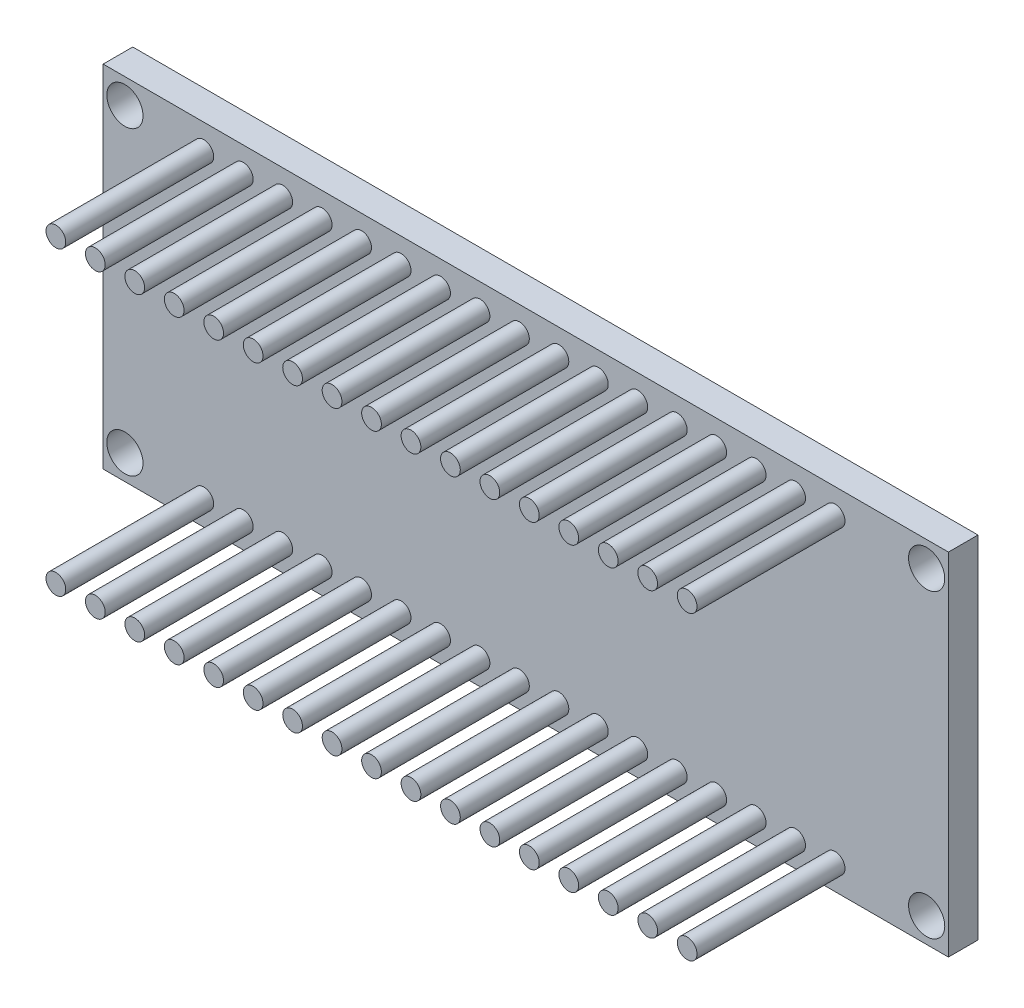
SolidWorks part; units mm, degrees
ref_plane "Front Plane" through (0, 0, 0) normal (0, 0, 1) x (1, 0, 0)
ref_plane "Top Plane" through (0, 0, 0) normal (0, 1, 0) x (1, 0, 0)
ref_plane "Right Plane" through (0, 0, 0) normal (1, 0, 0) x (0, 0, -1)
sketch "Sketch1" plane through (0, 0, 0) normal (0, 0, 1) x (1, 0, 0)
  line L0 (-219.0854, 61.6535) -> (-176.2406, 61.6535) construction
  line L1 (-176.2406, 70.5435) -> (-219.0854, 70.5435)
  line L2 (-176.2406, 70.5435) -> (-176.2406, 52.7635)
  line L3 (-176.2406, 52.7635) -> (-219.0854, 52.7635)
  line L4 (-219.0854, 70.5435) -> (-219.0854, 52.7635)
  line L5 (-197.663, 70.5435) -> (-197.663, 52.7635) construction
  circle A0 centre (-217.983, 69.2785) radius 0.9174
  circle A1 centre (-217.983, 54.0285) radius 0.9174
  circle A2 centre (-177.343, 54.0285) radius 0.9174
  circle A3 centre (-177.343, 69.2785) radius 0.9174
extrude "Boss-Extrude1" add sketch "Sketch1" along normal blind 1.5
sketch "Sketch2" plane through (0, 0, 1.5) normal (0, 0, 1) x (1, 0, 0)
  line L0 (-217.983, 69.2785) -> (-177.343, 69.2785) construction
  line L1 (-219.0854, 61.6535) -> (-203.7997, 61.6535) construction
  line L2 (-219.0854, 70.5435) -> (-219.0854, 52.7635) construction
  circle A0 centre (-213.983, 69.2785) radius 0.5
  circle A2 centre (-213.983, 54.0285) radius 0.5
  circle A3 centre (-211.983, 69.2785) radius 0.5
  circle A4 centre (-211.983, 54.0285) radius 0.5
  circle A5 centre (-209.983, 69.2785) radius 0.5
  circle A6 centre (-209.983, 54.0285) radius 0.5
  circle A7 centre (-207.983, 69.2785) radius 0.5
  circle A8 centre (-207.983, 54.0285) radius 0.5
  circle A9 centre (-205.983, 69.2785) radius 0.5
  circle A10 centre (-205.983, 54.0285) radius 0.5
  circle A11 centre (-203.983, 69.2785) radius 0.5
  circle A12 centre (-203.983, 54.0285) radius 0.5
  circle A13 centre (-201.983, 69.2785) radius 0.5
  circle A14 centre (-201.983, 54.0285) radius 0.5
  circle A15 centre (-199.983, 69.2785) radius 0.5
  circle A16 centre (-199.983, 54.0285) radius 0.5
  circle A17 centre (-197.983, 69.2785) radius 0.5
  circle A18 centre (-197.983, 54.0285) radius 0.5
  circle A19 centre (-195.983, 69.2785) radius 0.5
  circle A20 centre (-195.983, 54.0285) radius 0.5
  circle A21 centre (-193.983, 69.2785) radius 0.5
  circle A22 centre (-193.983, 54.0285) radius 0.5
  circle A23 centre (-191.983, 69.2785) radius 0.5
  circle A24 centre (-191.983, 54.0285) radius 0.5
  circle A25 centre (-189.983, 69.2785) radius 0.5
  circle A26 centre (-189.983, 54.0285) radius 0.5
  circle A27 centre (-187.983, 69.2785) radius 0.5
  circle A28 centre (-187.983, 54.0285) radius 0.5
  circle A29 centre (-185.983, 69.2785) radius 0.5
  circle A30 centre (-185.983, 54.0285) radius 0.5
  circle A31 centre (-183.983, 69.2785) radius 0.5
  circle A32 centre (-183.983, 54.0285) radius 0.5
  circle A33 centre (-181.983, 69.2785) radius 0.5
  circle A34 centre (-181.983, 54.0285) radius 0.5
  dimension "D1" = 17
extrude "Boss-Extrude2" add sketch "Sketch2" along normal blind 7.5
sketch "Sketch3" plane through (0, 0, 0) normal (0, 0, -1) x (-1, 0, 0)
  line L0 (219.0854, 61.6535) -> (176.2406, 61.6535) construction
  line L1 (219.0854, 70.5435) -> (219.0854, 52.7635) construction
  line L2 (176.2406, 52.7635) -> (176.2406, 70.5435) construction
  line L3 (215.3354, 65.1535) -> (220.3354, 65.1535)
  line L4 (215.3354, 65.1535) -> (215.3354, 58.1535)
  line L5 (215.3354, 58.1535) -> (220.3354, 58.1535)
  line L6 (220.3354, 65.1535) -> (220.3354, 58.1535)
extrude "Boss-Extrude3" add sketch "Sketch3" along normal blind 2
fillet "Fillet1" radius 0.75 4 edges at (-219.7104, 65.1535, 0) (-217.8354, 65.1535, -2) (-219.7104, 58.1535, 0) (-217.8354, 58.1535, -2)
